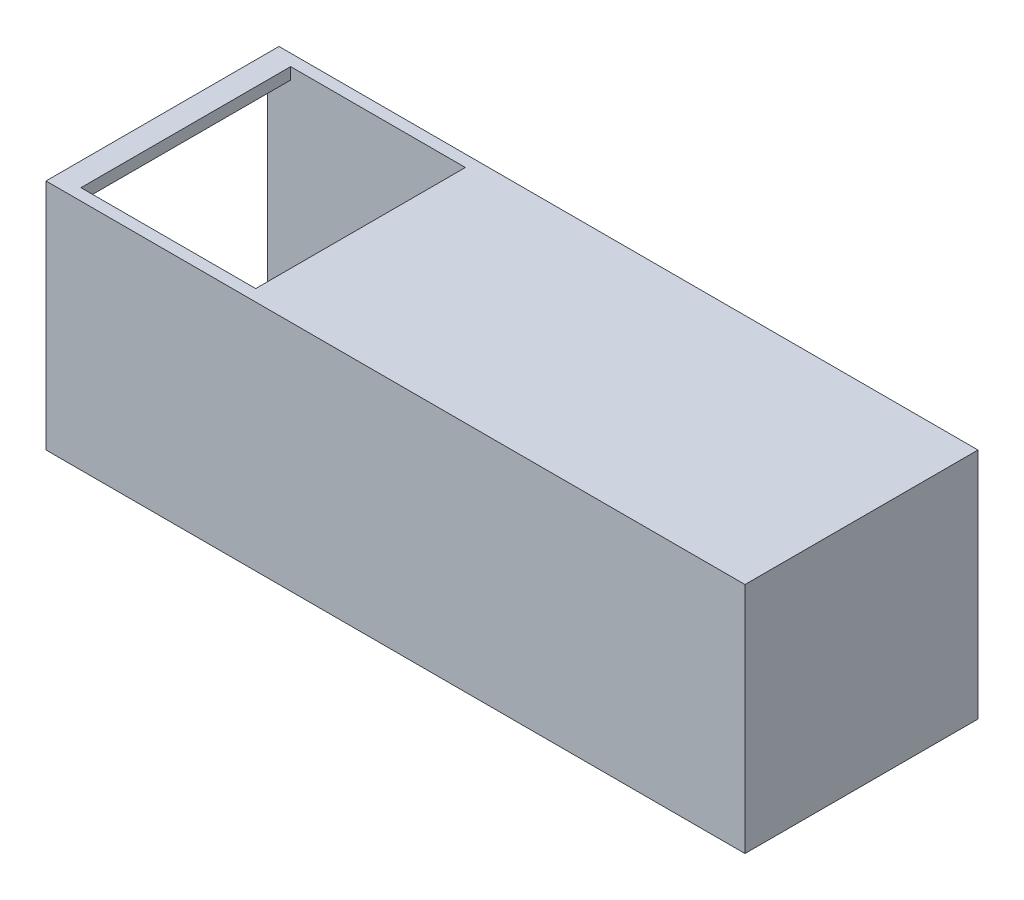
SolidWorks part; units mm, degrees
ref_plane "Front Plane" through (0, 0, 0) normal (0, 0, 1) x (1, 0, 0)
ref_plane "Top Plane" through (0, 0, 0) normal (0, 1, 0) x (1, 0, 0)
ref_plane "Right Plane" through (0, 0, 0) normal (1, 0, 0) x (0, 0, -1)
sketch "Sketch1" plane through (0, 0, 0) normal (0, 1, 0) x (1, 0, 0)
  line L1 (0, 0) -> (-120, 0)
  line L2 (0, 0) -> (0, 40)
  line L3 (0, 40) -> (-120, 40)
  line L4 (-120, 0) -> (-120, 40)
  dimension "D1" = 40
  dimension "D2" = 120
extrude "Boss-Extrude1" add sketch "Sketch1" along normal blind 40
shell "Shell1" thickness 2
sketch "Sketch2" plane through (0, 2, 0) normal (0, 1, 0) x (1, 0, 0)
  line L0 (-2, 2) -> (-2, 38) construction
  line L1 (-2, 38) -> (-120, 38) construction
  circle A0 centre (-20, 20) radius 18
  dimension "D1" = 36
extrude "Cut-Extrude1" cut sketch "Sketch2" against normal through all
sketch "Sketch3" plane through (0, 40, 0) normal (0, 1, 0) x (1, 0, 0)
  line L0 (-120, 0) -> (0, 0) construction
  line L1 (-116, 38) -> (-86, 38)
  line L2 (-116, 38) -> (-116, 2)
  line L3 (-116, 2) -> (-86, 2)
  line L4 (-86, 38) -> (-86, 2)
  line L6 (-120, 40) -> (-120, 0) construction
  line L7 (0, 40) -> (-120, 40) construction
  dimension "D1" = 4
  dimension "D2" = 30
  dimension "D3" = 2
  dimension "D4" = 2
extrude "Cut-Extrude2" cut sketch "Sketch3" against normal up to next
